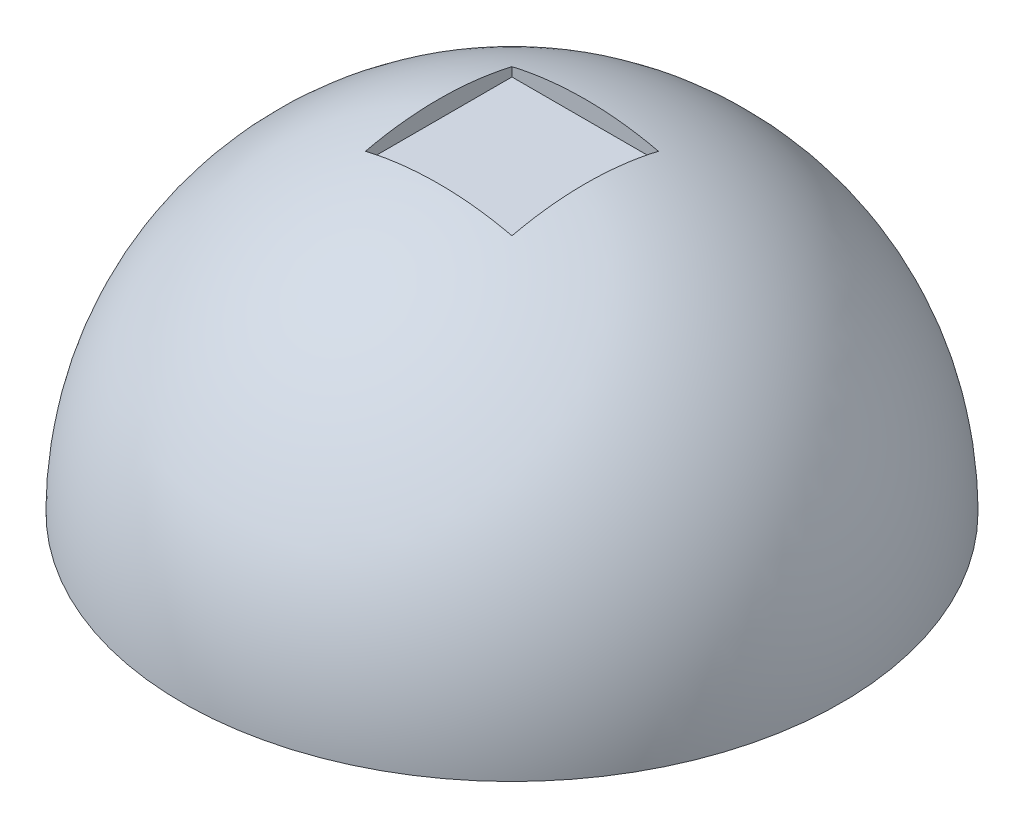
SolidWorks part; units mm, degrees
material "1.0035 (S185)"
ref_plane "Front Plane" through (0, 0, 0) normal (0, 0, 1) x (1, 0, 0)
ref_plane "Top Plane" through (0, 0, 0) normal (0, 1, 0) x (1, 0, 0)
ref_plane "Right Plane" through (0, 0, 0) normal (1, 0, 0) x (0, 0, -1)
sketch "Sketch1" plane through (0, 0, 0) normal (0, 0, 1) x (1, 0, 0)
  line L0 (0, 0) -> (228.6, 0)
  line L1 (0, 0) -> (0, 228.6)
  line L2 (0, 0) -> (0, 524.5675) construction
  arc A0 (228.6, 0) -> (0, 228.6) centre (0, 0) ccw
  dimension "D1" = 228.6
revolve "Revolve1" add sketch "Sketch1" angle 360 about L2
ref_plane "Plane1" through (0, 228.6, 0) normal (0, 1, 0) x (1, 0, 0)
sketch "Sketch2" plane through (0, 228.6, 0) normal (0, 1, 0) x (1, 0, 0)
  line L1 (-50.8, -50.8) -> (50.8, -50.8)
  line L2 (-50.8, -50.8) -> (-50.8, 50.8)
  line L3 (-50.8, 50.8) -> (50.8, 50.8)
  line L4 (50.8, -50.8) -> (50.8, 50.8)
  line L5 (-50.8, -50.8) -> (50.8, 50.8) construction
  line L6 (-50.8, 50.8) -> (50.8, -50.8) construction
  point P0 (0, 0)
  dimension "D1" = 50.8
  dimension "D2" = 50.8
extrude "Cut-Extrude1" cut sketch "Sketch2" against normal blind 17.78 contours L3 L4 L1 L2
sketch "Sketch3" plane through (0, 0, 0) normal (0, -1, 0) x (-1, 0, 0)
  point P0 (0, 0)
equation "\"D2@Sketch2\"=\"D1@Sketch2\""
